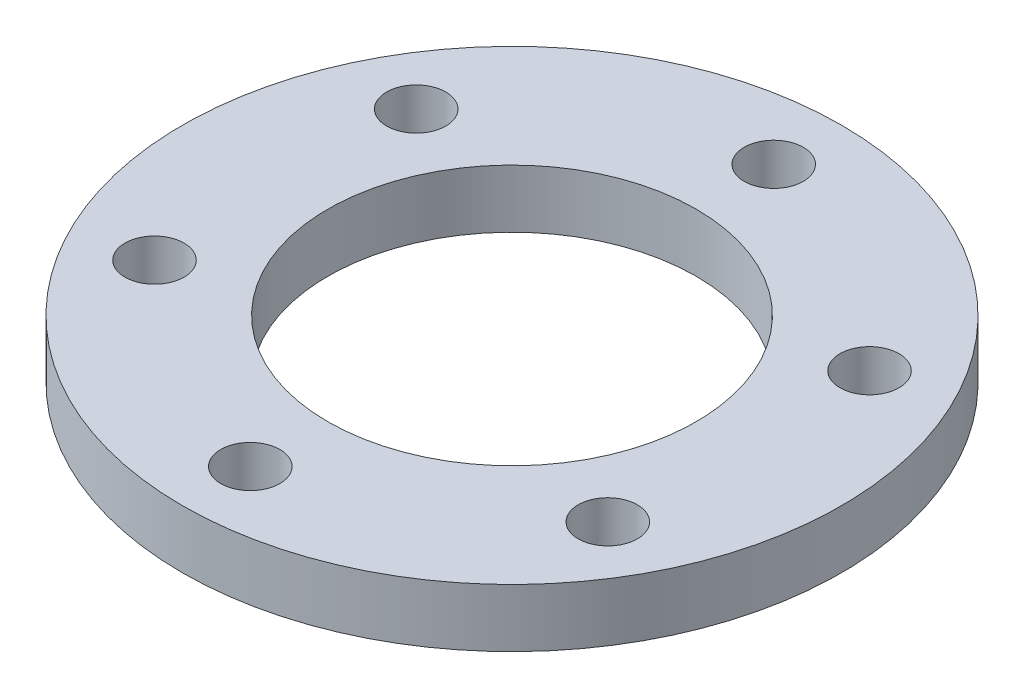
SolidWorks part; units mm, degrees
material "ABS"
ref_plane "前视基准面" through (0, 0, 0) normal (0, 0, 1) x (1, 0, 0)
ref_plane "上视基准面" through (0, 0, 0) normal (0, 1, 0) x (1, 0, 0)
ref_plane "右视基准面" through (0, 0, 0) normal (1, 0, 0) x (0, 0, -1)
other "Configuration Table"
sketch "草图1" plane through (0, 0, 0) normal (0, 1, 0) x (1, 0, 0)
  circle A0 centre (0, 0) radius 17
  circle A1 centre (0, 0) radius 9.5
  dimension "D1" = 19
  dimension "D2" = 34
extrude "凸台-拉伸1" add sketch "草图1" along normal blind 3
sketch "草图2" plane through (0, 3, 0) normal (0, 1, 0) x (1, 0, 0)
  circle A0 centre (0, 0) radius 13.5 construction
  circle A1 centre (0, 13.5) radius 1.525
  circle A2 centre (11.6913, 6.75) radius 1.525
  circle A3 centre (11.6913, -6.75) radius 1.525
  circle A4 centre (0, -13.5) radius 1.525
  circle A5 centre (-11.6913, -6.75) radius 1.525
  circle A6 centre (-11.6913, 6.75) radius 1.525
  point P17 (0, 0)
  dimension "D1" = 27
  dimension "D2" = 3.05
extrude "切除-拉伸1" cut sketch "草图2" against normal blind 100
